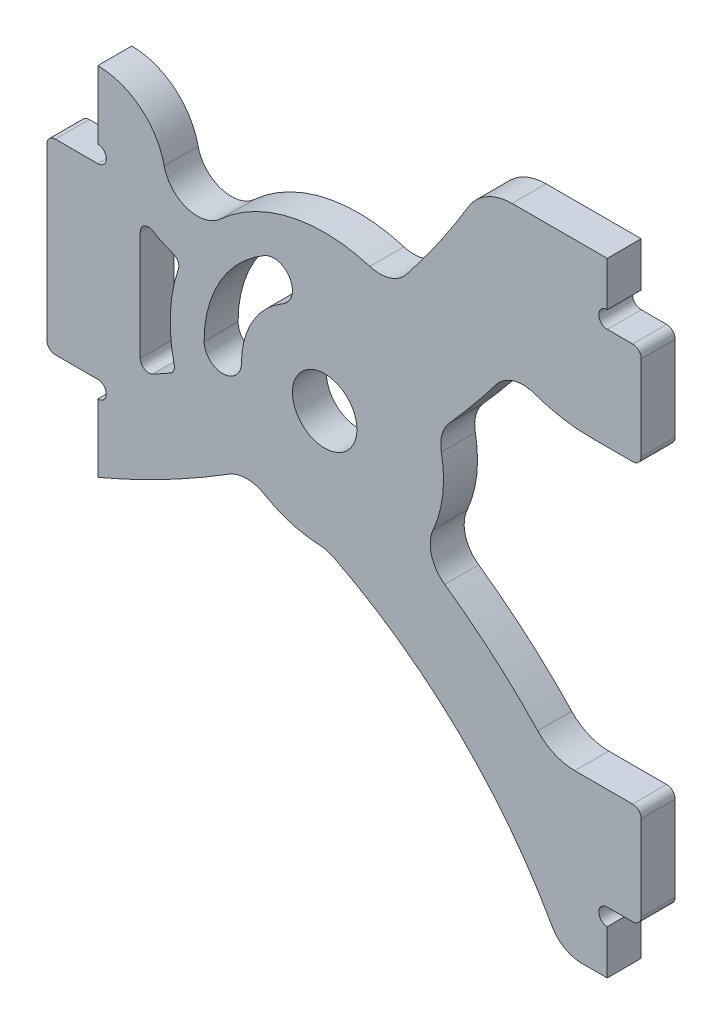
SolidWorks part; units mm, degrees
material "Thornel Mat VMA"
ref_plane "Front Plane" through (0, 0, 0) normal (0, 0, 1) x (1, 0, 0)
ref_plane "Top Plane" through (0, 0, 0) normal (0, 1, 0) x (1, 0, 0)
ref_plane "Right Plane" through (0, 0, 0) normal (1, 0, 0) x (0, 0, -1)
sketch "Sketch1" plane through (0, 0, 0) normal (0, 0, 1) x (1, 0, 0)
  line L0 (-10.8612, -2.7469) -> (-10.8612, 3.6982)
  line L1 (18.6388, -16.4828) -> (18.6388, -11.4828)
  line L2 (18.1388, -10.9828) -> (14.7268, -10.9828)
  line L3 (15.6388, 6.4809) -> (18.1388, 6.4809)
  line L4 (18.6388, 6.9809) -> (18.6388, 11.9809)
  line L5 (18.1388, 12.4809) -> (16.6388, 12.4809)
  line L6 (16.6388, 13.4809) -> (16.6388, 16.099)
  line L7 (16.6388, 16.099) -> (11.036, 16.099)
  line L8 (-13.3612, 10.9299) -> (-13.3612, 6.9299)
  line L9 (-13.3612, 5.9299) -> (-15.8612, 5.9299)
  line L10 (-16.3612, 5.4299) -> (-16.3612, -4.5701)
  line L11 (-15.8612, -5.0701) -> (-13.3612, -5.0701)
  line L12 (-13.3612, -6.0701) -> (-13.3612, -10.0701)
  line L13 (15.1341, -20.6008) -> (16.6388, -20.6008)
  line L14 (16.6388, -20.6008) -> (16.6388, -17.9828)
  line L15 (16.6388, -16.9828) -> (18.1388, -16.9828)
  arc A1 (-3.55, 6.1488) -> (-7.1, 0) centre (0, 0) ccw
  arc A2 (-2.45, 4.2435) -> (-3.55, 6.1488) centre (-3, 5.1962) ccw
  arc A3 (-2.45, 4.2435) -> (-4.9, 0) centre (0, 0) ccw
  arc A4 (-7.1, 0) -> (-4.9, 0) centre (-6, 0) ccw
  arc A5 (-8.6167, 2.9261) -> (-8.8612, -2.071) centre (0, 0) ccw
  arc A6 (-9.1006, -2.6193) -> (-8.8612, -2.071) centre (-9.3481, -2.1848) ccw
  arc A7 (-10.1235, -3.1868) -> (-9.1006, -2.6193) centre (-34.9514, 42.7712) ccw
  arc A8 (-10.8612, -2.7469) -> (-10.1235, -3.1868) centre (-10.3612, -2.7469) ccw
  arc A9 (-10.0884, 4.1173) -> (-10.8612, 3.6982) centre (-10.3612, 3.6982) ccw
  arc A10 (-10.0884, 4.1173) -> (-8.933, 3.5615) centre (-7.3612, 8.308) ccw
  arc A11 (-8.6167, 2.9261) -> (-8.933, 3.5615) centre (-9.0902, 3.0869) ccw
  arc A12 (18.1388, -16.9828) -> (18.6388, -16.4828) centre (18.1388, -16.4828) ccw
  arc A13 (18.6388, -11.4828) -> (18.1388, -10.9828) centre (18.1388, -11.4828) ccw
  arc A14 (12.546, -10.0428) -> (14.7268, -10.9828) centre (14.7268, -7.9828) ccw
  arc A15 (12.546, -10.0428) -> (7.0688, -5.3142) centre (-13.3612, -34.5151) ccw
  arc A16 (6.3897, -2.8587) -> (7.0688, -5.3142) centre (8.2153, -3.6755) ccw
  arc A17 (6.3897, -2.8587) -> (6.8712, 1.3367) centre (0, 0) ccw
  arc A18 (7.3418, 3.0498) -> (6.8712, 1.3367) centre (8.8344, 1.7186) ccw
  arc A19 (7.3418, 3.0498) -> (10.097, 6.3872) centre (-34.9514, 40.7712) ccw
  arc A20 (12.3671, 7.0545) -> (10.097, 6.3872) centre (11.6868, 5.1738) ccw
  arc A21 (12.3671, 7.0545) -> (15.6388, 6.4809) centre (15.6388, 16.099) ccw
  arc A22 (18.1388, 6.4809) -> (18.6388, 6.9809) centre (18.1388, 6.9809) ccw
  arc A23 (18.6388, 11.9809) -> (18.1388, 12.4809) centre (18.1388, 11.9809) ccw
  arc A24 (16.6388, 13.4809) -> (16.6388, 12.4809) centre (16.6388, 12.9809) ccw
  arc A25 (11.036, 16.099) -> (8.4655, 14.6458) centre (11.036, 13.099) ccw
  arc A26 (4.8203, 9.3741) -> (8.4655, 14.6458) centre (-34.9514, 40.7712) ccw
  arc A27 (2.6648, 8.7011) -> (4.8203, 9.3741) centre (3.2505, 10.6134) ccw
  arc A28 (2.6648, 8.7011) -> (-6.1442, 6.7126) centre (0, 0) ccw
  arc A29 (-9.4501, 7.7686) -> (-6.1442, 6.7126) centre (-7.4945, 8.1879) ccw
  arc A30 (-9.4501, 7.7686) -> (-13.3612, 10.9299) centre (-13.3612, 6.9299) ccw
  arc A31 (-13.3612, 5.9299) -> (-13.3612, 6.9299) centre (-13.3612, 6.4299) ccw
  arc A32 (-15.8612, 5.9299) -> (-16.3612, 5.4299) centre (-15.8612, 5.4299) ccw
  arc A33 (-16.3612, -4.5701) -> (-15.8612, -5.0701) centre (-15.8612, -4.5701) ccw
  arc A34 (-13.3612, -6.0701) -> (-13.3612, -5.0701) centre (-13.3612, -5.5701) ccw
  arc A35 (-13.3612, -10.0701) -> (-5.6459, -6.0493) centre (-34.9514, 40.7712) ccw
  arc A36 (-3.566, -6.0236) -> (-5.6459, -6.0493) centre (-4.5848, -7.7447) ccw
  arc A37 (-3.566, -6.0236) -> (-0.2891, -6.994) centre (0, 0) ccw
  arc A38 (0.5355, -7.2099) -> (-0.2891, -6.994) centre (-0.3717, -8.9923) ccw
  arc A39 (13.3879, -19.576) -> (0.5355, -7.2099) centre (-13.3612, -34.5151) ccw
  arc A40 (13.3879, -19.576) -> (15.1341, -20.6008) centre (15.1341, -18.6008) ccw
  arc A41 (16.6388, -16.9828) -> (16.6388, -17.9828) centre (16.6388, -17.4828) ccw
  dimension "D1" = 7
  dimension "D2" = 9.1
extrude "Boss-Extrude1" add sketch "Sketch1" along normal blind 2
hole_wizard "M3.5 Clearance Hole1" positions "Sketch2" profile "Sketch3" hole size "M3.5" standard "ANSI Metric" end condition up to next
sketch "Sketch2" plane through (0, 0, 0) normal (0, 0, -1) x (-1, 0, 0)
  point P0 (0, 0)
sketch "Sketch3" plane through (0, 0, 0) normal (1, 0, 0) x (0, 1, 0)
  line L0 (0, 0) -> (0, 2)
  line L1 (0, 2) -> (1.9, 2)
  line L2 (1.9, 2) -> (1.9, 0)
  line L5 (1.9, 0) -> (0, 0)
  line L11 (0, -6.35) -> (0, 107.95) construction
  dimension "Thru Hole Dia." = 3.8
  dimension "Thru Hole Depth" = 2
